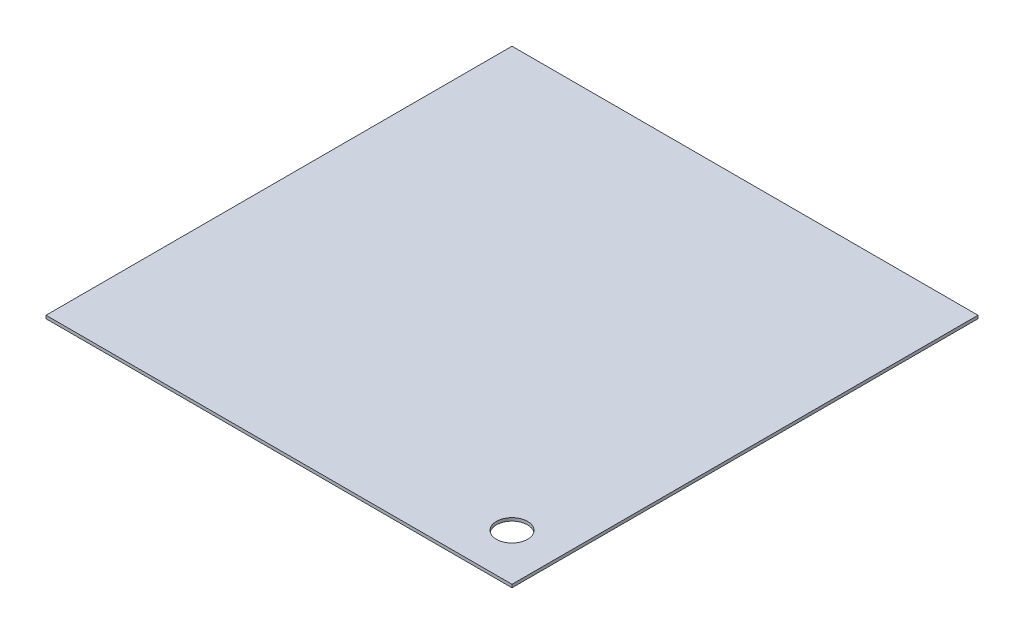
SolidWorks part; units mm, degrees
material "Cedar"
ref_plane "Front Plane" through (0, 0, 0) normal (0, 0, 1) x (1, 0, 0)
ref_plane "Top Plane" through (0, 0, 0) normal (0, 1, 0) x (1, 0, 0)
ref_plane "Right Plane" through (0, 0, 0) normal (1, 0, 0) x (0, 0, -1)
sketch "Sketch1" plane through (0, 0, 0) normal (0, 1, 0) x (1, 0, 0)
  line L1 (-190.0428, -190.0428) -> (190.0428, -190.0428)
  line L2 (-190.0428, -190.0428) -> (-190.0428, 190.0428)
  line L3 (-190.0428, 190.0428) -> (190.0428, 190.0428)
  line L4 (190.0428, -190.0428) -> (190.0428, 190.0428)
  line L5 (-190.0428, -190.0428) -> (190.0428, 190.0428) construction
  line L6 (-190.0428, 190.0428) -> (190.0428, -190.0428) construction
  point P0 (0, 0)
  dimension "D1" = 380.0856
extrude "Boss-Extrude1" add sketch "Sketch1" along normal blind 2.5
sketch "Sketch2" plane through (0, 2.5, 0) normal (0, 1, 0) x (1, 0, 0)
  line L0 (190.0428, -190.0428) -> (190.0428, 190.0428) construction
  line L1 (-190.0428, -190.0428) -> (190.0428, -190.0428) construction
  circle A0 centre (151.9428, -151.9428) radius 12.7
  dimension "D1" = 25.4
  dimension "D2" = 38.1
  dimension "D3" = 38.1
extrude "Cut-Extrude1" cut sketch "Sketch2" against normal through all
